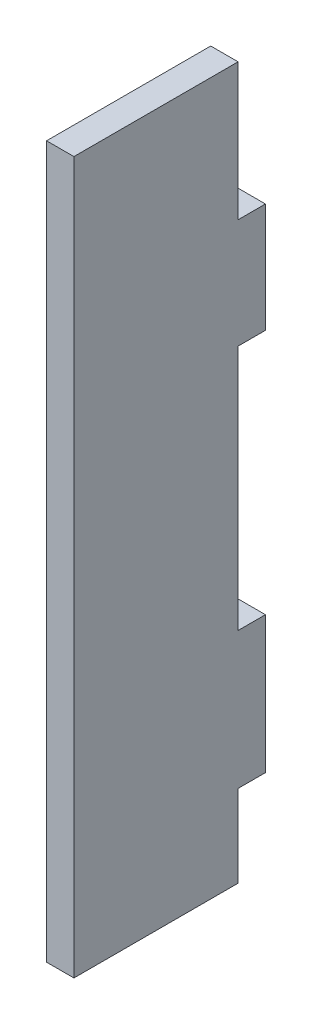
SolidWorks part; units mm, degrees
ref_plane "Front Plane" through (0, 0, 0) normal (0, 0, 1) x (1, 0, 0)
ref_plane "Top Plane" through (0, 0, 0) normal (0, 1, 0) x (1, 0, 0)
ref_plane "Right Plane" through (0, 0, 0) normal (1, 0, 0) x (0, 0, -1)
sketch "Sketch1" plane through (0, 0, 0) normal (0, 0, 1) x (1, 0, 0)
  line L4 (-20.3836, 25.8631) -> (-20.3836, 45.8631)
  line L5 (-25.3836, 25.8631) -> (-20.3836, 25.8631)
  line L6 (-25.3836, 45.8631) -> (-25.3836, 25.8631)
  line L7 (-20.3836, 45.8631) -> (-25.3836, 45.8631)
  line L12 (-25.3836, -19.1369) -> (-25.3836, -44.1369)
  line L13 (-20.3836, -19.1369) -> (-25.3836, -19.1369)
  line L14 (-20.3836, -44.1369) -> (-20.3836, -19.1369)
  line L15 (-25.3836, -44.1369) -> (-20.3836, -44.1369)
  dimension "D1" = 20
  dimension "D2" = 5
  dimension "D3" = 5
  dimension "D4" = 25
  dimension "D5" = 45
extrude "Boss-Extrude1" add sketch "Sketch1" along normal blind 5
sketch "Sketch2" plane through (0, 0, 5) normal (0, 0, 1) x (1, 0, 0)
  line L0 (-25.3836, 45.8631) -> (-25.3836, 25.8631) construction
  line L1 (-25.3836, 70.8631) -> (-20.3836, 70.8631)
  line L2 (-25.3836, 70.8631) -> (-25.3836, -59.1369)
  line L3 (-25.3836, -59.1369) -> (-20.3836, -59.1369)
  line L4 (-20.3836, 70.8631) -> (-20.3836, -59.1369)
  line L5 (-20.3836, 25.8631) -> (-20.3836, 45.8631) construction
  line L6 (-25.3836, -44.1369) -> (-20.3836, -44.1369) construction
  line L7 (-20.3836, 45.8631) -> (-25.3836, 45.8631) construction
  dimension "D1" = 15
  dimension "D2" = 25
extrude "Boss-Extrude2" add sketch "Sketch2" along normal blind 30
